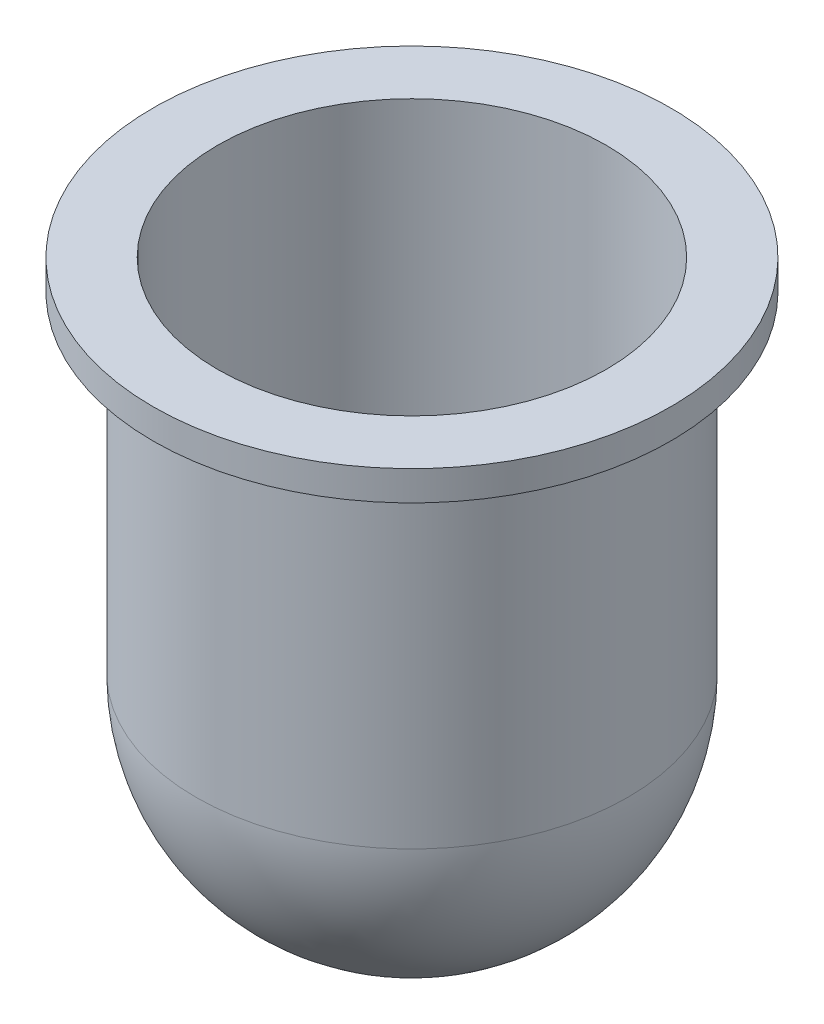
SolidWorks part; units mm, degrees
ref_plane "Front Plane" through (0, 0, 0) normal (0, 0, 1) x (1, 0, 0)
ref_plane "Top Plane" through (0, 0, 0) normal (0, 1, 0) x (1, 0, 0)
ref_plane "Right Plane" through (0, 0, 0) normal (1, 0, 0) x (0, 0, -1)
sketch "Sketch2" plane through (0, 0, 0) normal (0, 0, 1) x (1, 0, 0)
  line L0 (0, 107.0775) -> (0, -88.0328) construction
  line L2 (-13.5, 40) -> (-13.5, 15)
  line L3 (-15, 40) -> (-13.5, 40)
  line L4 (0, 0) -> (0, 1.5)
  line L5 (-15, 40) -> (-17.9858, 40)
  line L6 (-17.9858, 40) -> (-17.9858, 37.9356)
  line L7 (-17.9858, 37.9356) -> (-15, 37.9356)
  line L8 (-15, 37.9356) -> (-15, 15)
  line L9 (-15, 40) -> (-15, 15) construction
  arc A0 (-15, 15) -> (0, 0) centre (0, 15) ccw
  arc A1 (-13.5, 15) -> (0, 1.5) centre (0, 15) ccw
  point P5 (-15, 37.9356)
  dimension "D1" = 15
  dimension "D2" = 40
  dimension "D3" = 1.5
revolve "Revolve1" add sketch "Sketch2" angle 360 about L0
